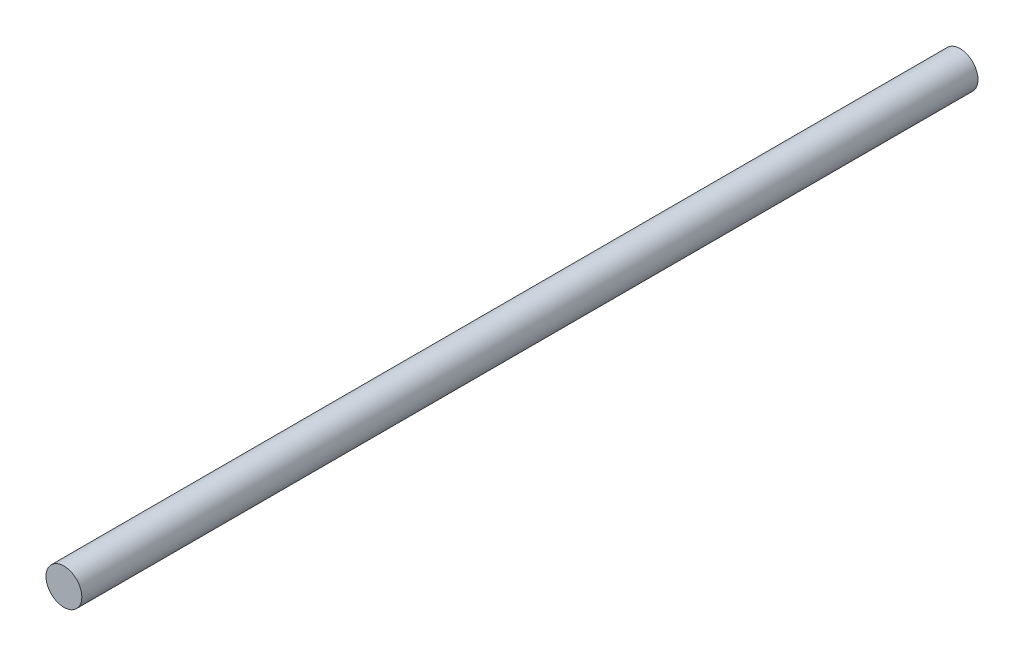
SolidWorks part; units mm, degrees
ref_plane "前视基准面" through (0, 0, 0) normal (0, 0, 1) x (1, 0, 0)
ref_plane "上视基准面" through (0, 0, 0) normal (0, 1, 0) x (1, 0, 0)
ref_plane "右视基准面" through (0, 0, 0) normal (1, 0, 0) x (0, 0, -1)
other "Configuration Table"
sketch "草图1" plane through (0, 0, 0) normal (0, 0, 1) x (1, 0, 0)
  circle A0 centre (0, 0) radius 2
extrude "凸台-拉伸1" add sketch "草图1" along normal blind 100
